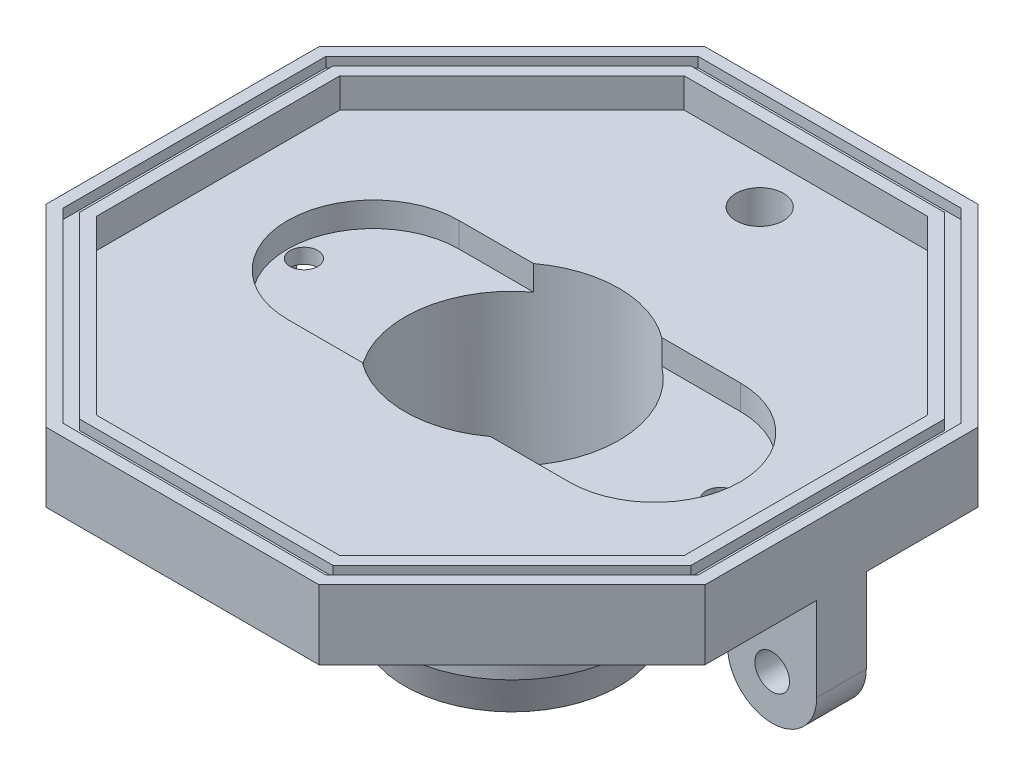
SolidWorks part; units mm, degrees
other "마크업1"
sketch "스케치18" plane through (34.9216, 6.2, -34.9216) normal (0.3551, 0.9348, -0.0006) x (0.8164, -0.3097, 0.4874)
other "마크업2"
sketch "스케치22" plane through (33.2597, -18, -33.2597) normal (0.2546, -0.4252, -0.8685) x (0.9614, 0.0144, 0.2748)
ref_plane "정면" through (0, 0, 0) normal (0, 0, 1) x (1, 0, 0)
ref_plane "윗면" through (0, 0, 0) normal (0, 1, 0) x (1, 0, 0)
ref_plane "우측면" through (0, 0, 0) normal (1, 0, 0) x (0, 0, -1)
sketch "스케치1" plane through (0, 0, 0) normal (0, 1, 0) x (1, 0, 0)
  line L0 (-55, 0) -> (55, 0) construction
  line L1 (13.2795, -32.0597) -> (32.0597, -13.2795)
  line L2 (32.0597, -13.2795) -> (32.0597, 13.2795)
  line L3 (32.0597, 13.2795) -> (13.2795, 32.0597)
  line L4 (13.2795, 32.0597) -> (-13.2795, 32.0597)
  line L5 (-13.2795, 32.0597) -> (-32.0597, 13.2795)
  line L6 (-32.0597, 13.2795) -> (-32.0597, -13.2795)
  line L7 (-32.0597, -13.2795) -> (-13.2795, -32.0597)
  line L8 (-13.2795, -32.0597) -> (13.2795, -32.0597)
  line L9 (13.7766, -33.2597) -> (33.2597, -13.7766)
  line L10 (33.2597, -13.7766) -> (33.2597, 13.7766)
  line L11 (33.2597, 13.7766) -> (13.7766, 33.2597)
  line L12 (13.7766, 33.2597) -> (-13.7766, 33.2597)
  line L13 (-13.7766, 33.2597) -> (-33.2597, 13.7766)
  line L14 (-33.2597, 13.7766) -> (-33.2597, -13.7766)
  line L15 (-33.2597, -13.7766) -> (-13.7766, -33.2597)
  line L16 (-13.7766, -33.2597) -> (13.7766, -33.2597)
  line L17 (12.7825, -30.8597) -> (30.8597, -12.7825)
  line L18 (30.8597, -12.7825) -> (30.8597, 12.7825)
  line L19 (30.8597, 12.7825) -> (12.7825, 30.8597)
  line L20 (12.7825, 30.8597) -> (-12.7825, 30.8597)
  line L21 (-12.7825, 30.8597) -> (-30.8597, 12.7825)
  line L22 (-30.8597, 12.7825) -> (-30.8597, -12.7825)
  line L23 (-30.8597, -12.7825) -> (-12.7825, -30.8597)
  line L24 (-12.7825, -30.8597) -> (12.7825, -30.8597)
  circle A0 centre (0, 0) radius 34.7011 construction
  dimension "D1" = 72
  dimension "D2" = 1.2
  dimension "D3" = 1.2
extrude "보스-돌출1" add sketch "스케치1" along normal blind 4 contours L14 L15 L16 L9 L10 L11 L12 L13
sketch "스케치2" plane through (0, 0, 0) normal (0, -1, 0) x (1, 0, 0)
  line L0 (0, -14.85) -> (0, 14.85) construction
  circle A0 centre (0, -25) radius 2.4
  dimension "D1" = 4.8
  dimension "D2" = 25
extrude "컷-돌출1" cut sketch "스케치2" against normal blind 4
sketch "스케치3" plane through (0, 4, 0) normal (0, 1, 0) x (1, 0, 0)
  line L24 (-12.2854, 29.6597) -> (-29.6597, 12.2854)
  line L25 (-29.6597, 12.2854) -> (-29.6597, -12.2854)
  line L26 (-29.6597, -12.2854) -> (-12.2854, -29.6597)
  line L27 (-12.2854, -29.6597) -> (12.2854, -29.6597)
  line L28 (12.2854, -29.6597) -> (29.6597, -12.2854)
  line L29 (29.6597, -12.2854) -> (29.6597, 12.2854)
  line L30 (29.6597, 12.2854) -> (12.2854, 29.6597)
  line L31 (12.2854, 29.6597) -> (-12.2854, 29.6597)
  line L32 (-12.2854, 29.6597) -> (-29.6597, 12.2854)
  line L33 (-29.6597, 12.2854) -> (-29.6597, -12.2854)
  line L34 (-29.6597, -12.2854) -> (-12.2854, -29.6597)
  line L35 (-12.2854, -29.6597) -> (12.2854, -29.6597)
  line L36 (12.2854, -29.6597) -> (29.6597, -12.2854)
  line L37 (29.6597, -12.2854) -> (29.6597, 12.2854)
  line L38 (29.6597, 12.2854) -> (12.2854, 29.6597)
  line L39 (12.2854, 29.6597) -> (-12.2854, 29.6597)
  line L48 (-13.7766, 33.2597) -> (-33.2597, 13.7766)
  line L49 (-33.2597, 13.7766) -> (-33.2597, -13.7766)
  line L50 (-33.2597, -13.7766) -> (-13.7766, -33.2597)
  line L51 (-13.7766, -33.2597) -> (13.7766, -33.2597)
  line L52 (13.7766, -33.2597) -> (33.2597, -13.7766)
  line L53 (33.2597, -13.7766) -> (33.2597, 13.7766)
  line L54 (33.2597, 13.7766) -> (13.7766, 33.2597)
  line L55 (13.7766, 33.2597) -> (-13.7766, 33.2597)
  line L56 (-13.7766, 33.2597) -> (-33.2597, 13.7766)
  line L57 (-33.2597, 13.7766) -> (-33.2597, -13.7766)
  line L58 (-33.2597, -13.7766) -> (-13.7766, -33.2597)
  line L59 (-13.7766, -33.2597) -> (13.7766, -33.2597)
  line L60 (13.7766, -33.2597) -> (33.2597, -13.7766)
  line L61 (33.2597, -13.7766) -> (33.2597, 13.7766)
  line L62 (33.2597, 13.7766) -> (13.7766, 33.2597)
  line L63 (13.7766, 33.2597) -> (-13.7766, 33.2597)
  dimension "D1" = 3.6
  dimension "D2" = 0
extrude "보스-돌출3" add sketch "스케치3" along normal blind 3
sketch "스케치5" plane through (0, 7, 0) normal (0, 1, 0) x (1, 0, 0)
  line L0 (12.7825, 30.8597) -> (-12.7825, 30.8597)
  line L1 (-12.7825, 30.8597) -> (-30.8597, 12.7825)
  line L2 (-30.8597, 12.7825) -> (-30.8597, -12.7825)
  line L3 (-30.8597, -12.7825) -> (-12.7825, -30.8597)
  line L4 (-12.7825, -30.8597) -> (12.7825, -30.8597)
  line L5 (12.7825, -30.8597) -> (30.8597, -12.7825)
  line L6 (30.8597, -12.7825) -> (30.8597, 12.7825)
  line L7 (30.8597, 12.7825) -> (12.7825, 30.8597)
  line L8 (13.2795, 32.0597) -> (-13.2795, 32.0597)
  line L9 (-13.2795, 32.0597) -> (-32.0597, 13.2795)
  line L10 (-32.0597, 13.2795) -> (-32.0597, -13.2795)
  line L11 (-32.0597, -13.2795) -> (-13.2795, -32.0597)
  line L12 (-13.2795, -32.0597) -> (13.2795, -32.0597)
  line L13 (13.2795, -32.0597) -> (32.0597, -13.2795)
  line L14 (32.0597, -13.2795) -> (32.0597, 13.2795)
  line L15 (32.0597, 13.2795) -> (13.2795, 32.0597)
  line L16 (13.7766, 33.2597) -> (-13.7766, 33.2597)
  line L17 (-13.7766, 33.2597) -> (-33.2597, 13.7766)
  line L18 (-33.2597, 13.7766) -> (-33.2597, -13.7766)
  line L19 (-33.2597, -13.7766) -> (-13.7766, -33.2597)
  line L20 (-13.7766, -33.2597) -> (13.7766, -33.2597)
  line L21 (13.7766, -33.2597) -> (33.2597, -13.7766)
  line L22 (33.2597, -13.7766) -> (33.2597, 13.7766)
  line L23 (33.2597, 13.7766) -> (13.7766, 33.2597)
  line L24 (13.7766, 33.2597) -> (-13.7766, 33.2597)
  line L25 (-13.7766, 33.2597) -> (-33.2597, 13.7766)
  line L26 (-33.2597, 13.7766) -> (-33.2597, -13.7766)
  line L27 (-33.2597, -13.7766) -> (-13.7766, -33.2597)
  line L28 (-13.7766, -33.2597) -> (13.7766, -33.2597)
  line L29 (13.7766, -33.2597) -> (33.2597, -13.7766)
  line L30 (33.2597, -13.7766) -> (33.2597, 13.7766)
  line L31 (33.2597, 13.7766) -> (13.7766, 33.2597)
  dimension "D1" = 0
  dimension "D2" = 1.2
  dimension "D3" = 1.2
extrude "컷-돌출2" cut sketch "스케치5" against normal blind 1 contours L14 L15 L8 L9 L10 L11 L12 L13 L7 L6 L5 L4 L3 L2 L1 L0
sketch "스케치7" plane through (0, 0, 0) normal (0, -1, 0) x (1, 0, 0)
  circle A0 centre (0, 0) radius 10.8
  dimension "D1" = 21.6
extrude "컷-돌출4" cut sketch "스케치7" against normal blind 4
sketch "스케치8" plane through (0, 0, 0) normal (0, -1, 0) x (1, 0, 0)
  circle A0 centre (0, 0) radius 10.8 construction
  circle A1 centre (0, 0) radius 10.8
  circle A2 centre (0, 0) radius 11.8
  dimension "D1" = 1
extrude "보스-돌출4" add sketch "스케치8" along normal blind 16.5
sketch "스케치9" plane through (0, -16.5, 0) normal (0, -1, 0) x (1, 0, 0)
  circle A0 centre (0, 0) radius 10.8 construction
  circle A1 centre (0, 0) radius 10.8
  circle A2 centre (0, 0) radius 6.05
  dimension "D1" = 12.1
extrude "보스-돌출5" add sketch "스케치9" along normal blind 3.5 separate body
sketch "스케치10" plane through (0, 0, 0) normal (0, 0, 1) x (1, 0, 0)
  line L0 (-11.8, -16.5) -> (-10.8, -20)
  line L1 (-10.8, -16.5) -> (-10.8, -20) construction
  line L2 (-10.8, -16.5) -> (-10.8, -20)
  line L4 (-11.8, -16.5) -> (-10.8, -16.5)
  dimension "D1" = 3.5
ref_axis "기준축1" through (0, -20, 0) along (0, 1, 0)
revolve "회전1" add sketch "스케치10" angle 360 about axis through (0, -20, 0) along (0, 1, 0)
sketch "스케치11" plane through (0, 4, 0) normal (0, 1, 0) x (1, 0, 0)
  line L3 (-14, 0) -> (14.4, 0) construction
  line L4 (-14, 8.65) -> (14.4, 8.65)
  line L5 (-14, -8.65) -> (14.4, -8.65)
  arc A2 (-14, 8.65) -> (-14, -8.65) centre (-14, 0) ccw
  arc A3 (14.4, -8.65) -> (14.4, 8.65) centre (14.4, 0) ccw
  point P10 (0.2, 0)
  dimension "D1" = 28.4
  dimension "D3" = 17.3
extrude "컷-돌출5" cut sketch "스케치11" against normal blind 2.5
sketch "스케치13" plane through (0, 0, 0) normal (0, -1, 0) x (1, 0, 0)
  line L0 (0, -3.85) -> (0, 3.85) construction
  line L1 (-33.2597, 2.5) -> (-24.2597, 2.5)
  line L2 (-33.2597, 2.5) -> (-33.2597, -2.5)
  line L3 (-33.2597, -2.5) -> (-24.2597, -2.5)
  line L4 (-24.2597, 2.5) -> (-24.2597, -2.5)
  line L5 (3.85, 0) -> (-3.85, 0) construction
  line L6 (-33.2597, -13.7766) -> (-33.2597, 13.7766) construction
  dimension "D1" = 2.5
  dimension "D2" = 5
  dimension "D3" = 9
extrude "보스-돌출7" add sketch "스케치13" along normal blind 8.5
sketch "스케치16" plane through (0, 1.5, 0) normal (0, 1, 0) x (1, 0, 0)
  circle A0 centre (-21, 0) radius 1.4
  dimension "D1" = 2.8
  dimension "D2" = 21
extrude "컷-돌출8" cut sketch "스케치16" against normal blind 10
mirror "대칭 복사2" about plane through (0, 0, 0) normal (1, 0, 0) of "컷-돌출8"
sketch "스케치19" plane through (0, -8.5, 0) normal (0, -1, 0) x (1, 0, 0)
  line L0 (-28.7597, 5.4405) -> (-28.7597, -5.7268) construction
  line L4 (-33.2597, 2.5) -> (-33.2597, -2.5)
  line L5 (-33.2597, -2.5) -> (-24.2597, -2.5)
  line L6 (-24.2597, -2.5) -> (-24.2597, 2.5)
  line L7 (-24.2597, 2.5) -> (-33.2597, 2.5)
  line L8 (-33.2597, 2.5) -> (-33.2597, -2.5)
  line L9 (-33.2597, -2.5) -> (-24.2597, -2.5)
  line L10 (-24.2597, -2.5) -> (-24.2597, 2.5)
  line L11 (-24.2597, 2.5) -> (-33.2597, 2.5)
  dimension "D2" = 4.5
  dimension "D1" = 0
revolve "회전2" add sketch "스케치19" angle 360 about L0
sketch "스케치20" plane through (0, 0, -2.5) normal (0, 0, -1) x (-1, 0, 0)
  line L0 (33.2597, -8.5) -> (33.2597, 0) construction
  circle A0 centre (28.7597, -8.5) radius 1.75
  dimension "D1" = 3.5
  dimension "D2" = 4.5
extrude "컷-돌출9" cut sketch "스케치20" against normal through all
mirror "대칭 복사3" about plane through (0, 0, 0) normal (1, 0, 0) of "회전2", "컷-돌출9", "보스-돌출7"
